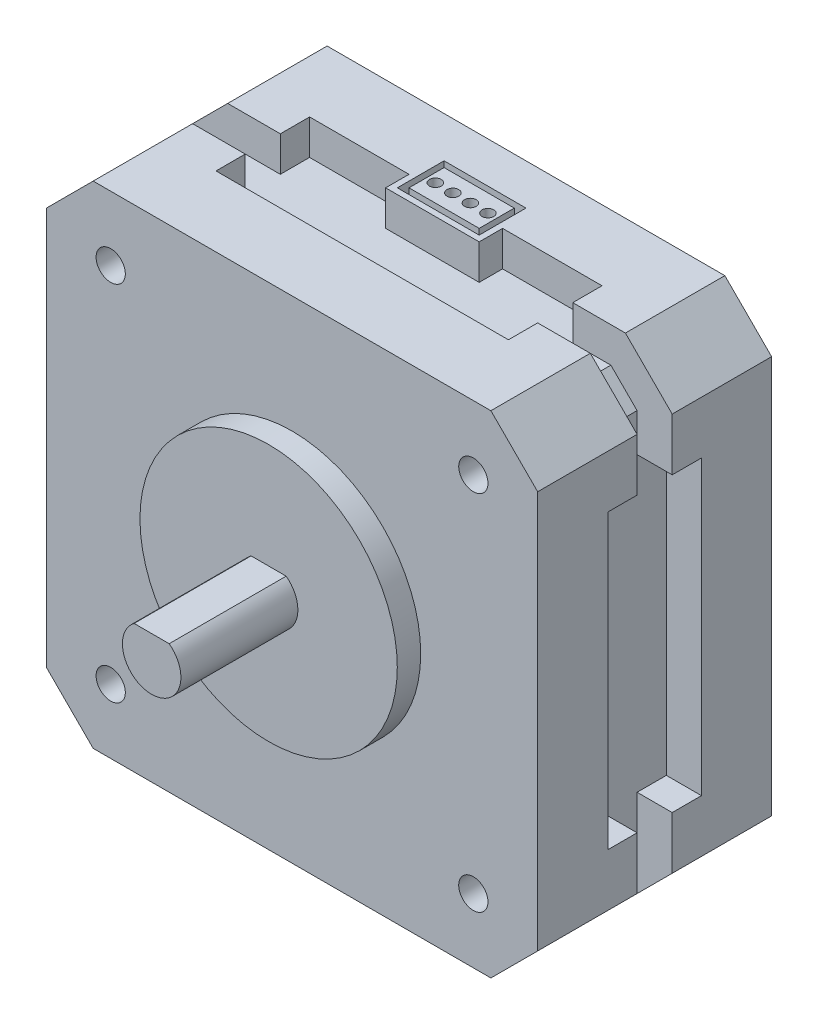
SolidWorks part; units mm, degrees
ref_plane "Front Plane" through (0, 0, 0) normal (0, 0, 1) x (1, 0, 0)
ref_plane "Top Plane" through (0, 0, 0) normal (0, 1, 0) x (1, 0, 0)
ref_plane "Right Plane" through (0, 0, 0) normal (1, 0, 0) x (0, 0, -1)
sketch "Sketch1" plane through (0, 0, 0) normal (0, 0, 1) x (1, 0, 0)
  line L0 (-21, 21) -> (-21, -21)
  line L1 (-21, -21) -> (21, -21)
  line L2 (21, -21) -> (21, 21)
  line L3 (21, 21) -> (-21, 21)
  point P2 (0, 21)
  point P5 (-21, 0)
  dimension "D1" = 42
extrude "Boss-Extrude1" add sketch "Sketch1" along normal mid plane 20
sketch "Sketch2" plane through (0, 0, 0) normal (0, 0, 1) x (1, 0, 0)
  line L0 (-15.5, 15.5) -> (-15.5, -15.5) construction
  line L1 (-15.5, -15.5) -> (15.5, -15.5) construction
  circle A0 centre (-15.5, 15.5) radius 1
  circle A1 centre (15.5, 15.5) radius 1
  circle A2 centre (15.5, -15.5) radius 1
  circle A3 centre (-15.5, -15.5) radius 1
  point P8 (0, -15.5)
  point P9 (-15.5, 0)
  dimension "D1" = 2
  dimension "D2" = 31
  dimension "D3" = 31
chamfer "Chamfer1" distance 4 angle 45 4 edges at (-21, -21, 0) (21, -21, 0) (21, 21, 0) (-21, 21, 0)
sketch "Sketch7" plane through (0, 0, 0) normal (0, 0, 1) x (1, 0, 0)
  line L36 (-21, 17) -> (-21, -17)
  line L37 (-21, -17) -> (-17, -21)
  line L38 (-17, -21) -> (17, -21)
  line L39 (17, -21) -> (21, -17)
  line L40 (21, -17) -> (21, 17)
  line L41 (21, 17) -> (17, 21)
  line L42 (17, 21) -> (-17, 21)
  line L43 (-17, 21) -> (-21, 17)
  line L44 (-18, 15.7574) -> (-18, -15.7574)
  line L45 (-18, -15.7574) -> (-15.7574, -18)
  line L46 (-15.7574, -18) -> (15.7574, -18)
  line L47 (15.7574, -18) -> (18, -15.7574)
  line L48 (18, -15.7574) -> (18, 15.7574)
  line L49 (18, 15.7574) -> (15.7574, 18)
  line L50 (15.7574, 18) -> (-15.7574, 18)
  line L51 (-15.7574, 18) -> (-18, 15.7574)
  line L52 (-18, 15.7574) -> (-18, -15.7574)
  line L53 (-18, -15.7574) -> (-15.7574, -18)
  line L54 (-15.7574, -18) -> (15.7574, -18)
  line L55 (15.7574, -18) -> (18, -15.7574)
  line L56 (18, -15.7574) -> (18, 15.7574)
  line L57 (18, 15.7574) -> (15.7574, 18)
  line L58 (15.7574, 18) -> (-15.7574, 18)
  line L59 (-15.7574, 18) -> (-18, 15.7574)
  dimension "D1" = 3
extrude "Cut-Extrude1" cut sketch "Sketch7" against normal mid plane 3
sketch "Sketch8" plane through (0, 0, 0) normal (0, 0, 1) x (1, 0, 0)
  line L0 (-12.5, 21) -> (-12.5, 18)
  line L1 (17, 21) -> (-17, 21) construction
  line L2 (-12.5, 18) -> (12.5, 18)
  line L3 (12.5, 18) -> (12.5, 21)
  line L4 (12.5, 21) -> (-12.5, 21)
  line L5 (-21, 0) -> (21, 0) construction
  line L6 (-21, 17) -> (-21, -17) construction
  line L7 (21, -17) -> (21, 17) construction
  line L8 (0, 21) -> (0, -21) construction
  line L9 (-17, -21) -> (17, -21) construction
  line L10 (-21, 12.5) -> (-18, 12.5)
  line L11 (-18, 12.5) -> (-18, -12.5)
  line L12 (-18, -12.5) -> (-21, -12.5)
  line L13 (-21, -12.5) -> (-21, 12.5)
  line L14 (12.5, -21) -> (-12.5, -21)
  line L15 (12.5, -18) -> (12.5, -21)
  line L16 (-12.5, -18) -> (12.5, -18)
  line L17 (-12.5, -21) -> (-12.5, -18)
  line L18 (21, -12.5) -> (21, 12.5)
  line L19 (18, -12.5) -> (21, -12.5)
  line L20 (18, 12.5) -> (18, -12.5)
  line L21 (21, 12.5) -> (18, 12.5)
  point P4 (0, 18)
  point P20 (-18, 0)
  dimension "D1" = 3
  dimension "D2" = 25
extrude "Cut-Extrude2" cut sketch "Sketch8" against normal mid plane 8
sketch "Sketch9" plane through (0, 0, 0) normal (0, 1, 0) x (1, 0, 0)
  line L0 (-4, 4) -> (-4, 2)
  line L1 (-12.5, 4) -> (12.5, 4) construction
  line L2 (-4, 2) -> (4, 2)
  line L3 (4, 2) -> (4, 4)
  line L4 (4, 4) -> (-4, 4)
  point P4 (0, 2)
  dimension "D1" = 8
  dimension "D2" = 2
extrude "Boss-Extrude2" add sketch "Sketch9" along normal up to surface (3 mm away) from surface at 18 up to face at (0, 21, -4.25) starting at face at (0, 18, 0)
sketch "Sketch10" plane through (0, 21, 0) normal (0, 1, 0) x (1, 0, 0)
  line L7 (-3.5, 6.5) -> (3.5, 6.5)
  line L8 (-3, 6) -> (3, 6)
  line L9 (3, 6) -> (3, 3)
  line L10 (3.5, 4) -> (3.5, 2.5)
  line L11 (3.5, 2.5) -> (-3.5, 2.5)
  line L12 (-3.5, 2.5) -> (-3.5, 4)
  line L13 (3.5, 6.5) -> (3.5, 2.5)
  line L14 (3.5, 2.5) -> (-3.5, 2.5)
  line L15 (-3.5, 2.5) -> (-3.5, 6.5)
  line L16 (3, 3) -> (-3, 3)
  line L17 (-3, 3) -> (-3, 6)
  line L18 (-2.25, 4.5) -> (-0.75, 4.5) construction
  line L19 (-0.75, 4.5) -> (0.75, 4.5) construction
  line L20 (0.75, 4.5) -> (2.25, 4.5) construction
  circle A0 centre (-2.25, 4.5) radius 0.5
  circle A1 centre (-0.75, 4.5) radius 0.5
  circle A2 centre (0.75, 4.5) radius 0.5
  circle A3 centre (2.25, 4.5) radius 0.5
  point P18 (0, 4.5)
  point P21 (-3, 4.5)
  dimension "D3" = 0.5
  dimension "D4" = 1
  dimension "D2" = 4
  dimension "D5" = 1.5
  dimension "D1" = 0.5
extrude "Cut-Extrude3" cut sketch "Sketch10" against normal blind 3 contours L15 L14 L13 L7 L16 L17 L8 L9 | A1 | A2 | A3 | A0
sketch "Sketch11" plane through (0, 0, 10) normal (0, 0, 1) x (1, 0, 0)
  circle A0 centre (0, 0) radius 11
  dimension "D1" = 22
extrude "Boss-Extrude3" add sketch "Sketch11" along normal blind 2
sketch "Sketch12" plane through (0, 0, 12) normal (0, 0, 1) x (1, 0, 0)
  line L0 (1.5, 2) -> (-1.5, 2)
  line L1 (17, 21) -> (-17, 21) construction
  arc A0 (-1.5, 2) -> (1.5, 2) centre (0, 0) ccw
  dimension "D1" = 5
  dimension "D2" = 2
extrude "Boss-Extrude4" add sketch "Sketch12" along normal blind 20
hole_wizard "Tap Drill for M3x0.5 Tap2" positions "Sketch13" profile "Sketch14" hole size "M3x0.5" standard "ANSI Metric" end condition through all
sketch "Sketch13" plane through (0, 0, 10) normal (0, 0, 1) x (1, 0, 0)
  point P0 (-15.5, 15.5)
  point P3 (15.5, 15.5)
  point P6 (15.5, -15.5)
  point P9 (-15.5, -15.5)
sketch "Sketch14" plane through (-15.5, 15.5, 10) normal (1, 0, 0) x (0, -1, 0)
  line L0 (0, 0) -> (0, 20)
  line L1 (0, 20) -> (1.25, 20)
  line L2 (1.25, 20) -> (1.25, 0)
  line L5 (1.25, 0) -> (0, 0)
  line L11 (0, -6.35) -> (0, 107.95) construction
  dimension "Thru Hole Dia." = 2.5
  dimension "Thru Hole Depth" = 20
sketch "Sketch15" plane through (0, 0, -10) normal (0, 0, -1) x (-1, 0, 0)
  circle A0 centre (-15.5, 15.5) radius 3
  circle A1 centre (15.5, 15.5) radius 3
  circle A2 centre (15.5, -15.5) radius 3
  circle A3 centre (-15.5, -15.5) radius 3
  circle A4 centre (0, 0) radius 6
  circle A5 centre (0, 0) radius 4
  dimension "D1" = 6
  dimension "D2" = 12
  dimension "D3" = 8
extrude "Cut-Extrude4" cut sketch "Sketch15" against normal blind 3
sketch "Sketch16" plane through (0, 0, -7) normal (0, 0, -1) x (-1, 0, 0)
  circle A4 centre (-15.5, 15.5) radius 2.75
  circle A5 centre (15.5, 15.5) radius 2.75
  circle A6 centre (15.5, -15.5) radius 2.75
  circle A7 centre (-15.5, -15.5) radius 2.75
extrude "Boss-Extrude5" add sketch "Sketch16" along normal blind 3 separate body
fillet "Fillet1" radius 2 1 edges at (12.75, 15.5, -10)
fillet "Fillet2" radius 2 1 edges at (-18.25, 15.5, -10)
fillet "Fillet3" radius 2 1 edges at (-18.25, -15.5, -10)
fillet "Fillet4" radius 2 1 edges at (12.75, -15.5, -10)
sketch "Sketch17" plane through (0, 0, -10) normal (0, 0, -1) x (-1, 0, 0)
  line L0 (-15.75, 14.25) -> (-15.75, 13.2505)
  line L1 (-15.25, 14.25) -> (-15.25, 13.2505)
  line L2 (-15.75, 17.7226) -> (-15.75, 16.75)
  line L3 (-17.7375, 15.25) -> (-16.75, 15.25)
  line L4 (-15.25, 17.7226) -> (-15.25, 16.75)
  line L5 (-17.7345, 15.75) -> (-16.75, 15.75)
  line L6 (0, 21) -> (0, -21) construction
  line L7 (-17, 21) -> (17, 21) construction
  line L8 (17, -21) -> (-17, -21) construction
  line L9 (-21, 0) -> (21, 0) construction
  line L10 (-21, -17) -> (-21, 17) construction
  line L11 (21, 17) -> (21, -17) construction
  line L12 (-14.25, 15.75) -> (-13.2655, 15.75)
  line L13 (-14.25, -15.25) -> (-13.2625, -15.25)
  line L14 (-14.25, 15.25) -> (-13.2625, 15.25)
  line L15 (-14.25, -15.75) -> (-13.2655, -15.75)
  line L16 (-17.7345, -15.75) -> (-16.75, -15.75)
  line L17 (-15.25, -17.7226) -> (-15.25, -16.75)
  line L18 (-17.7375, -15.25) -> (-16.75, -15.25)
  line L19 (-15.75, -17.7226) -> (-15.75, -16.75)
  line L20 (-15.25, -14.25) -> (-15.25, -13.2505)
  line L21 (-15.75, -14.25) -> (-15.75, -13.2505)
  line L22 (15.75, -14.25) -> (15.75, -13.2505)
  line L23 (15.25, -14.25) -> (15.25, -13.2505)
  line L24 (15.75, -17.7226) -> (15.75, -16.75)
  line L25 (17.7375, -15.25) -> (16.75, -15.25)
  line L26 (15.25, -17.7226) -> (15.25, -16.75)
  line L27 (17.7345, -15.75) -> (16.75, -15.75)
  line L28 (14.25, -15.75) -> (13.2655, -15.75)
  line L29 (14.25, 15.25) -> (13.2625, 15.25)
  line L30 (14.25, -15.25) -> (13.2625, -15.25)
  line L31 (14.25, 15.75) -> (13.2655, 15.75)
  line L32 (17.7345, 15.75) -> (16.75, 15.75)
  line L33 (15.25, 17.7226) -> (15.25, 16.75)
  line L34 (17.7375, 15.25) -> (16.75, 15.25)
  line L35 (15.75, 17.7226) -> (15.75, 16.75)
  line L36 (15.25, 14.25) -> (15.25, 13.2505)
  line L37 (15.75, 14.25) -> (15.75, 13.2505)
  arc A1 (-15.75, 13.2505) -> (-15.25, 13.2505) centre (-15.5, 15.4866) ccw
  arc A2 (-13.2625, 15.25) -> (-13.2655, 15.75) centre (-15.5, 15.4866) ccw
  arc A3 (-15.25, 17.7226) -> (-15.75, 17.7226) centre (-15.5, 15.4866) ccw
  arc A4 (-17.7345, 15.75) -> (-17.7375, 15.25) centre (-15.5, 15.4866) ccw
  arc A5 (-17.7345, -15.75) -> (-17.7375, -15.25) centre (-15.5, -15.4866) cw
  arc A6 (-15.25, -17.7226) -> (-15.75, -17.7226) centre (-15.5, -15.4866) cw
  arc A7 (-13.2625, -15.25) -> (-13.2655, -15.75) centre (-15.5, -15.4866) cw
  arc A8 (-15.75, -13.2505) -> (-15.25, -13.2505) centre (-15.5, -15.4866) cw
  arc A9 (15.75, -13.2505) -> (15.25, -13.2505) centre (15.5, -15.4866) ccw
  arc A10 (13.2625, -15.25) -> (13.2655, -15.75) centre (15.5, -15.4866) ccw
  arc A11 (15.25, -17.7226) -> (15.75, -17.7226) centre (15.5, -15.4866) ccw
  arc A12 (17.7345, -15.75) -> (17.7375, -15.25) centre (15.5, -15.4866) ccw
  arc A13 (17.7345, 15.75) -> (17.7375, 15.25) centre (15.5, 15.4866) cw
  arc A14 (15.25, 17.7226) -> (15.75, 17.7226) centre (15.5, 15.4866) cw
  arc A15 (13.2625, 15.25) -> (13.2655, 15.75) centre (15.5, 15.4866) cw
  arc A16 (15.75, 13.2505) -> (15.25, 13.2505) centre (15.5, 15.4866) cw
  arc A17 (-15.75, -14.25) -> (-16.75, -15.25) centre (-16.75, -14.25) cw
  arc A18 (-15.25, -14.25) -> (-14.25, -15.25) centre (-14.25, -14.25) ccw
  arc A19 (-14.25, -15.75) -> (-15.25, -16.75) centre (-14.25, -16.75) ccw
  arc A20 (-15.75, -16.75) -> (-16.75, -15.75) centre (-16.75, -16.75) ccw
  arc A21 (14.25, -15.25) -> (15.25, -14.25) centre (14.25, -14.25) ccw
  arc A22 (15.75, -14.25) -> (16.75, -15.25) centre (16.75, -14.25) ccw
  arc A23 (16.75, -15.75) -> (15.75, -16.75) centre (16.75, -16.75) ccw
  arc A24 (15.25, -16.75) -> (14.25, -15.75) centre (14.25, -16.75) ccw
  arc A25 (14.25, 15.75) -> (15.25, 16.75) centre (14.25, 16.75) ccw
  arc A26 (15.75, 16.75) -> (16.75, 15.75) centre (16.75, 16.75) ccw
  arc A27 (16.75, 15.25) -> (15.75, 14.25) centre (16.75, 14.25) ccw
  arc A28 (15.25, 14.25) -> (14.25, 15.25) centre (14.25, 14.25) ccw
  arc A29 (-16.75, 15.25) -> (-15.75, 14.25) centre (-16.75, 14.25) cw
  arc A30 (-15.25, 14.25) -> (-14.25, 15.25) centre (-14.25, 14.25) cw
  arc A31 (-14.25, 15.75) -> (-15.25, 16.75) centre (-14.25, 16.75) cw
  arc A32 (-15.75, 16.75) -> (-16.75, 15.75) centre (-16.75, 16.75) cw
  point P67 (-15.75, -15.25)
  point P70 (-15.25, -15.25)
  point P73 (-15.25, -15.75)
  point P76 (-15.75, -15.75)
  point P79 (15.25, -15.25)
  point P82 (15.75, -15.25)
  point P85 (15.75, -15.75)
  point P88 (15.25, -15.75)
  point P91 (15.25, 15.75)
  point P94 (15.75, 15.75)
  point P97 (15.75, 15.25)
  point P100 (15.25, 15.25)
  point P103 (-15.75, 15.25)
  point P106 (-15.25, 15.25)
  point P109 (-15.25, 15.75)
  point P112 (-15.75, 15.75)
  dimension "D1" = 4.5
  dimension "D2" = 1
extrude "Cut-Extrude5" cut sketch "Sketch17" against normal blind 2
fillet "Fillet5" radius 0.5 2 edges at (-4, 0, -10) (-6, 0, -10)
sketch "Sketch18" plane through (0, 0, 32) normal (0, 0, 1) x (1, 0, 0)
  line L1 (1.5, 2) -> (-1.5, 2)
  line L2 (1.5, 2) -> (-1.5, 2)
  arc A1 (-1.5, 2) -> (1.5, 2) centre (0, 0) ccw
  arc A2 (-1.5, 2) -> (1.5, 2) centre (0, 0) ccw
  dimension "D1" = 0
extrude "Cut-Extrude6" cut sketch "Sketch18" against normal blind 10
equation "\"`0\"=20"
